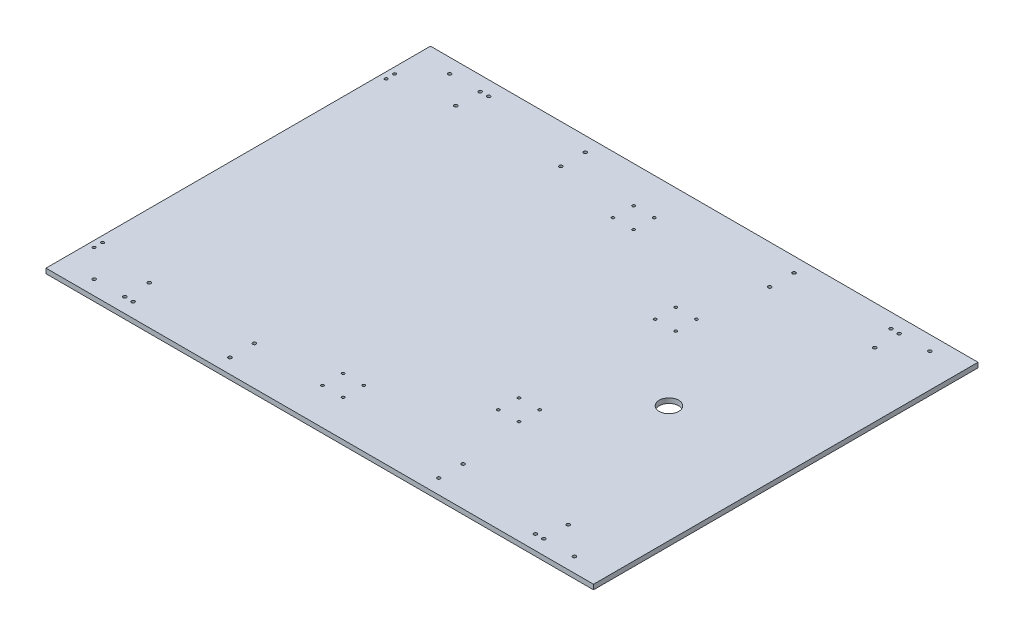
SolidWorks part; units mm, degrees
material "6061-T6 (SS)"
ref_plane "Front Plane" through (0, 0, 0) normal (0, 0, 1) x (1, 0, 0)
ref_plane "Top Plane" through (0, 0, 0) normal (0, 1, 0) x (1, 0, 0)
ref_plane "Right Plane" through (0, 0, 0) normal (1, 0, 0) x (0, 0, -1)
sketch "Sketch1" plane through (0, 0, 0) normal (0, 1, 0) x (1, 0, 0)
  line L1 (-357.1875, -250.825) -> (357.1875, -250.825)
  line L2 (-357.1875, -250.825) -> (-357.1875, 250.825)
  line L3 (-357.1875, 250.825) -> (357.1875, 250.825)
  line L4 (357.1875, -250.825) -> (357.1875, 250.825)
  line L5 (-357.1875, -250.825) -> (357.1875, 250.825) construction
  line L6 (-357.1875, 250.825) -> (357.1875, -250.825) construction
  point P0 (0, 0)
  dimension "D1" = 501.65
  dimension "D2" = 714.375
extrude "Boss-Extrude1" add sketch "Sketch1" along normal blind 6.35
sketch "Sketch2" plane through (0, 6.35, 0) normal (0, 1, 0) x (1, 0, 0)
  line L0 (0, 250.825) -> (0, -250.825) construction
  line L1 (357.1875, 250.825) -> (-357.1875, 250.825) construction
  line L2 (-357.1875, -250.825) -> (357.1875, -250.825) construction
  line L3 (-357.1875, 0) -> (357.1875, 0) construction
  line L4 (-357.1875, 250.825) -> (-357.1875, -250.825) construction
  line L5 (357.1875, -250.825) -> (357.1875, 250.825) construction
  line L6 (-357.1875, -246.0625) -> (357.1875, -246.0625) construction
  line L7 (-357.1875, 246.0625) -> (357.1875, 246.0625) construction
  line L8 (-352.425, 250.825) -> (-352.425, -250.825) construction
  line L9 (352.425, 250.825) -> (352.425, -250.825) construction
  line L10 (-352.425, -182.5625) -> (352.425, -182.5625) construction
  line L11 (0, -182.5625) -> (0, -246.0625) construction
  line L12 (-352.425, -214.3125) -> (0, -214.3125) construction
  line L13 (-114.3, -214.3125) -> (114.3, -214.3125) construction
  line L14 (-228.6, -214.3125) -> (228.6, -214.3125) construction
  line L15 (-228.6, 214.3125) -> (228.6, 214.3125) construction
  line L16 (-114.3, 214.3125) -> (114.3, 214.3125) construction
  line L17 (-352.425, 214.3125) -> (0, 214.3125) construction
  line L18 (0, 182.5625) -> (0, 246.0625) construction
  line L19 (-352.425, 182.5625) -> (352.425, 182.5625) construction
  line L20 (-357.1875, 246.0625) -> (357.1875, 246.0625) construction
  circle A0 centre (-114.3, -214.3125) radius 2.1527
  circle A1 centre (-228.6, -214.3125) radius 2.1527
  circle A2 centre (228.6, -214.3125) radius 2.1527
  circle A3 centre (114.3, -214.3125) radius 2.1527
  circle A4 centre (114.3, 214.3125) radius 2.1527
  circle A5 centre (228.6, 214.3125) radius 2.1527
  circle A6 centre (-228.6, 214.3125) radius 2.1527
  circle A7 centre (-114.3, 214.3125) radius 2.1527
  dimension "D6" = 4.3053
  dimension "D1" = 4.7625
  dimension "D2" = 4.7625
  dimension "D3" = 63.5
  dimension "D4" = 114.3
  dimension "D5" = 228.6
extrude "Cut-Extrude1" cut sketch "Sketch2" against normal through all
sketch "Sketch3" plane through (0, 6.35, 0) normal (0, 1, 0) x (1, 0, 0)
  line L0 (0, 250.825) -> (0, -250.825) construction
  line L1 (357.1875, 250.825) -> (-357.1875, 250.825) construction
  line L2 (-357.1875, -250.825) -> (357.1875, -250.825) construction
  line L3 (-357.1875, 0) -> (357.1875, 0) construction
  line L4 (-357.1875, 250.825) -> (-357.1875, -250.825) construction
  line L5 (357.1875, -250.825) -> (357.1875, 250.825) construction
  line L6 (0, 114.554) -> (357.1875, 114.554) construction
  line L7 (284.6388, 114.554) -> (284.6388, 0) construction
  line L8 (289.56, 0) -> (289.56, -177.8) construction
  line L9 (0, 250.825) -> (357.1875, 250.825) construction
  line L10 (178.5937, 250.825) -> (178.5937, -250.825) construction
  line L11 (289.56, 114.554) -> (289.56, 0) construction
  line L12 (280.9875, 114.554) -> (280.9875, 0) construction
  line L13 (280.9875, 0) -> (280.9875, -177.8) construction
  line L14 (76.2, 0) -> (76.2, -177.8) construction
  line L15 (76.2, 114.554) -> (76.2, 0) construction
  line L16 (67.6275, 114.554) -> (67.6275, 0) construction
  line L17 (67.6275, 0) -> (67.6275, -177.8) construction
  line L18 (72.5487, 114.554) -> (72.5487, 0) construction
  line L19 (-72.5487, 114.554) -> (-72.5487, 0) construction
  line L20 (-67.6275, 0) -> (-67.6275, -177.8) construction
  line L21 (-67.6275, 114.554) -> (-67.6275, 0) construction
  line L22 (-76.2, 114.554) -> (-76.2, 0) construction
  line L23 (-76.2, 0) -> (-76.2, -177.8) construction
  line L24 (-280.9875, 0) -> (-280.9875, -177.8) construction
  line L25 (-280.9875, 114.554) -> (-280.9875, 0) construction
  line L26 (-289.56, 114.554) -> (-289.56, 0) construction
  line L27 (-178.5938, 250.825) -> (-178.5938, -250.825) construction
  line L28 (-289.56, 0) -> (-289.56, -177.8) construction
  line L29 (-284.6388, 114.554) -> (-284.6388, 0) construction
  circle A0 centre (289.56, -152.4) radius 2.1526
  circle A1 centre (76.2, 101.6) radius 2.1526
  circle A2 centre (289.56, -50.8) radius 2.1526
  circle A3 centre (289.56, 50.8) radius 2.1526
  circle A4 centre (289.56, 152.4) radius 2.1526
  circle A5 centre (280.9875, -101.6) radius 2.1526
  circle A6 centre (280.9875, 0) radius 2.1526
  circle A7 centre (280.9875, 101.6) radius 2.1526
  circle A8 centre (76.2, 0) radius 2.1526
  circle A9 centre (76.2, -101.6) radius 2.1526
  circle A10 centre (67.6275, 152.4) radius 2.1526
  circle A11 centre (67.6275, 50.8) radius 2.1526
  circle A12 centre (67.6275, -50.8) radius 2.1526
  circle A13 centre (67.6275, -152.4) radius 2.1526
  circle A14 centre (-67.6275, -152.4) radius 2.1526
  circle A15 centre (-67.6275, -50.8) radius 2.1526
  circle A16 centre (-67.6275, 50.8) radius 2.1526
  circle A17 centre (-67.6275, 152.4) radius 2.1526
  circle A18 centre (-76.2, -101.6) radius 2.1526
  circle A19 centre (-76.2, 0) radius 2.1526
  circle A20 centre (-280.9875, 101.6) radius 2.1526
  circle A21 centre (-280.9875, 0) radius 2.1526
  circle A22 centre (-280.9875, -101.6) radius 2.1526
  circle A23 centre (-289.56, 152.4) radius 2.1526
  circle A24 centre (-289.56, 50.8) radius 2.1526
  circle A25 centre (-289.56, -50.8) radius 2.1526
  circle A26 centre (-76.2, 101.6) radius 2.1526
  circle A27 centre (-289.56, -152.4) radius 2.1526
  dimension "D8" = 101.6
  dimension "D5" = 3.6512
  dimension "D7" = 25.4
  dimension "D6" = 177.8
  dimension "D9" = 50.8
  dimension "D10" = 4.3053
  dimension "D14" = 4.3053
  dimension "D1" = 114.554
  dimension "D2" = 106.045
  dimension "D3" = 177.8
  dimension "D4" = 4.9213
  dimension "D11" = 4
  dimension "D12" = 101.6
  dimension "D13" = 101.6
extrude "Cut-Extrude3" [suppressed] cut sketch "Sketch3" against normal up to next
sketch "Sketch4" plane through (0, 0, 250.825) normal (0, 0, 1) x (1, 0, 0)
  line L1 (-357.1875, 0) -> (357.1875, 0)
  line L2 (-357.1875, 0) -> (-357.1875, 6.35)
  line L3 (-357.1875, 6.35) -> (357.1875, 6.35)
  line L4 (357.1875, 0) -> (357.1875, 6.35)
extrude "Boss-Extrude2" add sketch "Sketch4" against normal through all
hole_wizard "#8 Clearance Hole1" positions "Sketch7" profile "Sketch6" hole size "#8" standard "ANSI Inch"
sketch "Sketch7" plane through (0, 6.35, 0) normal (0, 1, 0) x (1, 0, 0)
  line L0 (357.1875, 250.825) -> (-357.1875, 250.825) construction
  line L1 (-357.1875, 250.825) -> (-357.1875, -250.825) construction
  line L2 (357.1875, -250.825) -> (357.1875, 250.825) construction
  line L3 (-357.1875, -250.825) -> (357.1875, -250.825) construction
  point P0 (-273.3675, 231.775)
  point P2 (-136.2075, 231.775)
  point P4 (136.2075, 231.775)
  point P6 (273.3675, 231.775)
  point P8 (273.3675, 200.025)
  point P10 (136.2075, 200.025)
  point P12 (-136.2075, 200.025)
  point P14 (-273.3675, 200.025)
  point P16 (-273.3675, -200.025)
  point P18 (-273.3675, -231.775)
  point P20 (-136.2075, -231.775)
  point P22 (-136.2075, -200.025)
  point P24 (136.2075, -200.025)
  point P26 (136.2075, -231.775)
  point P28 (273.3675, -231.775)
  point P30 (273.3675, -200.025)
  dimension "D1" = 19.05
  dimension "D2" = 83.82
  dimension "D3" = 83.82
  dimension "D4" = 19.05
  dimension "D5" = 137.16
  dimension "D6" = 31.75
  dimension "D7" = 137.16
  dimension "D8" = 31.75
sketch "Sketch6" plane through (-273.3675, 6.35, -231.775) normal (1, 0, 0) x (0, 0, 1)
  line L0 (0, 0) -> (0, 75.7154)
  line L1 (0, 75.7154) -> (2.1526, 74.422)
  line L2 (2.1526, 74.422) -> (2.1526, 0)
  line L5 (2.1526, 0) -> (0, 0)
  line L10 (0, 75.7154) -> (-2.1527, 74.422) construction
  line L11 (0, -6.35) -> (0, 107.95) construction
  dimension "Hole Dia." = 4.3053
  dimension "Hole Depth" = 74.422
  dimension "Drill Angle" = 118
hole_wizard "#8 Clearance Hole2" positions "Sketch9" profile "Sketch8" hole size "#8" standard "ANSI Inch"
sketch "Sketch9" plane through (0, 6.35, 0) normal (0, 1, 0) x (1, 0, 0)
  line L0 (357.1875, 250.825) -> (-357.1875, 250.825) construction
  line L1 (357.1875, -250.825) -> (357.1875, 250.825) construction
  line L2 (-357.1875, -250.825) -> (357.1875, -250.825) construction
  line L3 (-357.1875, 250.825) -> (-357.1875, -250.825) construction
  point P0 (-313.309, 231.9325)
  point P2 (313.309, 231.9325)
  point P4 (313.309, -231.9325)
  point P6 (-313.309, -231.9325)
  dimension "D1" = 18.8925
  dimension "D2" = 43.8785
  dimension "D3" = 18.8925
  dimension "D4" = 43.8785
  dimension "D5" = 43.8785
  dimension "D6" = 18.8925
  dimension "D7" = 18.8925
  dimension "D8" = 43.8785
sketch "Sketch8" plane through (-313.309, 6.35, -231.9325) normal (1, 0, 0) x (0, 0, 1)
  line L0 (0, 0) -> (0, 75.7154)
  line L1 (0, 75.7154) -> (2.1526, 74.422)
  line L2 (2.1526, 74.422) -> (2.1526, 0)
  line L5 (2.1526, 0) -> (0, 0)
  line L10 (0, 75.7154) -> (-2.1527, 74.422) construction
  line L11 (0, -6.35) -> (0, 107.95) construction
  dimension "Hole Dia." = 4.3053
  dimension "Hole Depth" = 74.422
  dimension "Drill Angle" = 118
sketch "Sketch11" plane through (0, 6.35, 0) normal (0, 1, 0) x (1, 0, 0)
  line L0 (136.2075, 200.025) -> (273.3675, -200.025) construction
  line L1 (273.3675, -200.025) -> (136.2075, -200.025) construction
  line L2 (136.2075, -200.025) -> (273.3675, 200.025) construction
  circle A0 centre (204.7875, 0) radius 12.7
extrude "Cut-Extrude4" cut sketch "Sketch11" against normal blind 83.82
hole_wizard "#6 Clearance Hole1" positions "Sketch13" profile "Sketch12" hole size "#6" standard "ANSI Inch"
sketch "Sketch13" plane through (0, 6.35, 0) normal (0, 1, 0) x (1, 0, 0)
  line L0 (-357.1875, 250.825) -> (-357.1875, -250.825) construction
  line L2 (-349.1357, -184.9209) -> (-349.1357, -196.0791) construction
  line L5 (-349.1357, 196.0791) -> (-349.1357, 184.9209) construction
  line L9 (-349.1357, -190.5) -> (-350.6671, -190.5) construction
  line L12 (-349.1357, 190.5) -> (-349.9602, 190.5) construction
  line L15 (-357.1875, -250.825) -> (357.1875, -250.825) construction
  line L16 (357.1875, 250.825) -> (-357.1875, 250.825) construction
  point P0 (-349.1357, 196.0791)
  point P2 (-349.1357, 184.9209)
  point P4 (-349.1357, -184.9209)
  point P6 (-349.1357, -196.0791)
  dimension "D1" = 11.1582
  dimension "D2" = 11.1582
  dimension "D3" = 8.0518
  dimension "D4" = 60.325
  dimension "D5" = 60.325
sketch "Sketch12" plane through (-349.1357, 6.35, -196.0791) normal (1, 0, 0) x (0, 0, 1)
  line L0 (0, 0) -> (0, 75.5628)
  line L1 (0, 75.5628) -> (1.8986, 74.422)
  line L2 (1.8986, 74.422) -> (1.8986, 0)
  line L5 (1.8986, 0) -> (0, 0)
  line L10 (0, 75.5628) -> (-1.8987, 74.422) construction
  line L11 (0, -6.35) -> (0, 107.95) construction
  dimension "Hole Dia." = 3.7973
  dimension "Hole Depth" = 74.422
  dimension "Drill Angle" = 118
sketch "Sketch14" plane through (0, 0, 0) normal (0, -1, 0) x (1, 0, 0)
  circle A0 centre (-44.3314, 202.9544) radius 1.778
  circle A1 centre (-17.3906, 202.9544) radius 1.778
  circle A2 centre (-17.3906, 176.0136) radius 1.778
  circle A3 centre (-44.3314, 176.0136) radius 1.778
  circle A4 centre (124.9129, 115.7689) radius 1.778
  circle A5 centre (124.9121, 88.8289) radius 1.7791
  circle A6 centre (97.9721, 88.8281) radius 1.778
  circle A7 centre (97.9721, 115.7689) radius 1.778
  circle A8 centre (97.9721, -88.8281) radius 1.778
  circle A9 centre (124.9129, -88.8281) radius 1.778
  circle A10 centre (124.9129, -115.7689) radius 1.778
  circle A11 centre (97.9721, -115.7689) radius 1.778
  circle A12 centre (-44.3314, -176.0136) radius 1.778
  circle A13 centre (-17.3906, -176.0136) radius 1.778
  circle A14 centre (-17.3906, -202.9544) radius 1.778
  circle A15 centre (-44.3314, -202.9544) radius 1.778
extrude "Cut-Extrude5" cut sketch "Sketch14" against normal blind 7.62
sketch "Sketch15" plane through (0, 6.35, 0) normal (0, 1, 0) x (1, 0, 0)
  circle A0 centre (-262.509, 231.9338) radius 2.1526
  circle A1 centre (262.509, 231.9338) radius 2.1526
  circle A2 centre (262.509, -231.9338) radius 2.1526
  circle A3 centre (-262.509, -231.9338) radius 2.1526
extrude "Cut-Extrude6" cut sketch "Sketch15" against normal blind 6.35
